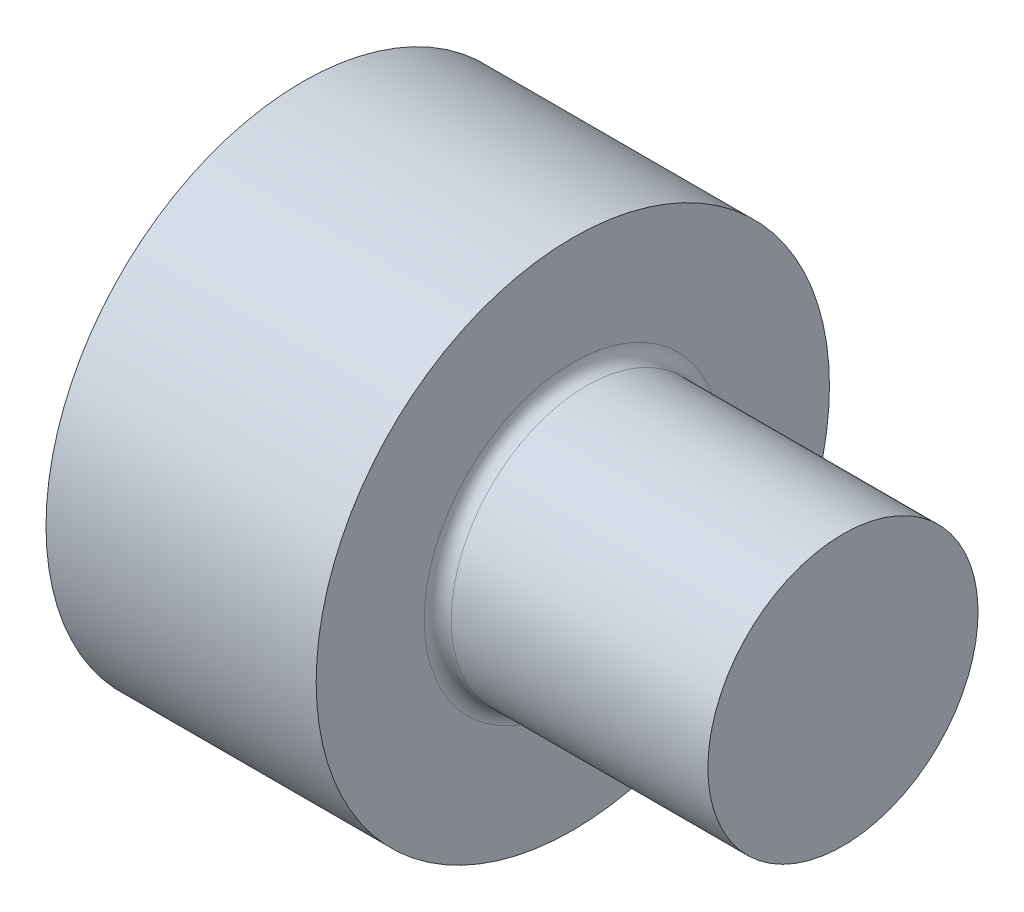
SolidWorks part; units mm, degrees
ref_plane "Front Plane" through (0, 0, 0) normal (0, 0, 1) x (1, 0, 0)
ref_plane "Top Plane" through (0, 0, 0) normal (0, 1, 0) x (1, 0, 0)
ref_plane "Right Plane" through (0, 0, 0) normal (1, 0, 0) x (0, 0, -1)
sketch "Sketch1" plane through (0, 0, 0) normal (0, 0, 1) x (1, 0, 0)
  line L0 (0, 0) -> (-40, 0)
  line L1 (-40, 0) -> (-40, 19)
  line L2 (-40, 19) -> (-20, 19)
  line L3 (-20, 19) -> (-20, 10)
  line L4 (-20, 10) -> (0, 10)
  line L5 (0, 10) -> (0, 0)
revolve "Revolve1" add sketch "Sketch1" angle 360 about L0
fillet "Fillet1" radius 1 1 edges at (-20, 10, 0)
